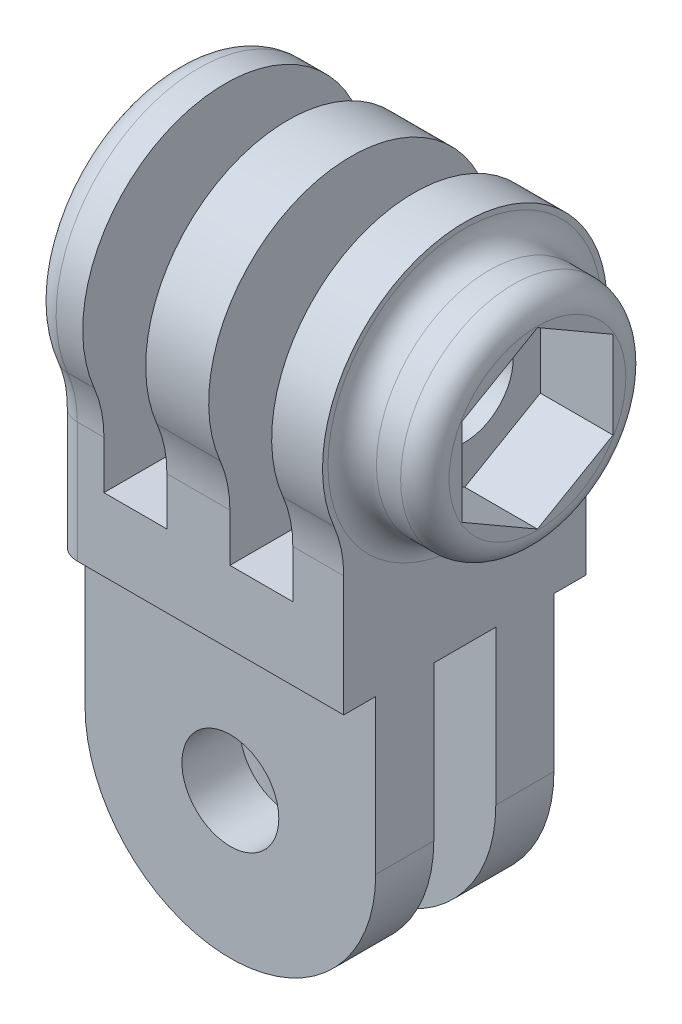
SolidWorks part; units mm, degrees
material "ABS"
ref_plane "Front Plane" through (0, 0, 0) normal (0, 0, 1) x (1, 0, 0)
ref_plane "Top Plane" through (0, 0, 0) normal (0, 1, 0) x (1, 0, 0)
ref_plane "Right Plane" through (0, 0, 0) normal (1, 0, 0) x (0, 0, -1)
sketch "Sketch1" plane through (0, 0, 0) normal (1, 0, 0) x (0, 0, -1)
  line L0 (-6.35, 0) -> (-4.6736, 0)
  line L1 (-6.35, 0) -> (-6.35, 6.3197)
  line L2 (6.35, 0) -> (6.35, 6.3197)
  line L3 (0, 0) -> (0, -15.7) construction
  line L4 (-1.6256, 0) -> (-1.6256, -15.7)
  line L5 (1.6256, 0) -> (1.6256, -15.7)
  line L6 (-4.6736, 0) -> (-4.6736, -15.7)
  line L7 (4.6736, 0) -> (4.6736, -15.7)
  line L8 (-4.6736, -15.7) -> (-1.6256, -15.7)
  line L9 (1.6256, -15.7) -> (4.6736, -15.7)
  line L10 (-1.6256, 0) -> (1.6256, 0)
  line L11 (4.6736, 0) -> (6.35, 0)
  circle A0 centre (0, 11.7475) radius 2.54
  arc A1 (6.8609, 8.8153) -> (-6.8609, 8.8153) centre (0, 11.7475) ccw
  arc A2 (6.8609, 8.8153) -> (6.35, 6.3197) centre (12.7, 6.3197) ccw
  arc A3 (-6.8609, 8.8153) -> (-6.35, 6.3197) centre (-12.7, 6.3197) cw
  dimension "D2" = 5.08
  dimension "D4" = 14.9225
  dimension "D5" = 6.35
  dimension "D1" = 12.7
  dimension "D3" = 11.7475
  dimension "D8" = 3.048
  dimension "D9" = 3.048
  dimension "D10" = 15.7
  dimension "D11" = 6.35
  dimension "D6" = 1.6256
  dimension "D7" = 1.6256
extrude "Boss-Extrude1" add sketch "Sketch1" against normal blind 15.24
sketch "Sketch2" plane through (0, 0, 4.6736) normal (0, 0, 1) x (1, 0, 0)
  line L0 (-7.62, 0) -> (-7.62, -15.7) construction
  line L1 (-15.24, 0) -> (0, 0) construction
  line L4 (-15.24, -8.08) -> (-15.24, 0)
  line L5 (-15.24, 0) -> (0, 0)
  line L6 (0, 0) -> (0, -8.08)
  line L7 (-15.24, -15.7) -> (0, -15.7) construction
  circle A0 centre (-7.62, -8.08) radius 2.54
  arc A1 (-15.24, -8.08) -> (0, -8.08) centre (-7.62, -8.08) ccw
  point P4 (-7.62, -15.7)
  line M1 (0, -15.7) -> (0, 0)
  line M3 (-15.24, 0) -> (-15.24, -15.7)
  line M4 (-15.24, -15.7) -> (0, -15.7)
  dimension "D1" = 5.08
extrude "Cut-Extrude1" cut sketch "Sketch2" against normal through all contours L0 A0 | A0 L0 | A1 M3 M4 | A1 M4 M1
sketch "Sketch3" plane through (0, 0, 0) normal (0, 0, 1) x (1, 0, 0)
  line L0 (0, 3.81) -> (-15.24, 3.81) construction
  line L1 (0, 6.3197) -> (0, 0) construction
  line L2 (-15.24, 6.3197) -> (-15.24, 0) construction
  line L3 (-15.24, 0) -> (0, 0) construction
  line L4 (-7.62, 3.81) -> (-7.62, 19.2088) construction
  line L5 (0, 19.2088) -> (-15.24, 19.2088) construction
  line L6 (-5.969, 3.81) -> (-5.969, 19.2088)
  line L7 (-9.271, 3.81) -> (-9.271, 19.2088)
  line L8 (-9.271, 19.2088) -> (-12.573, 19.2088)
  line L9 (-9.271, 3.81) -> (-12.573, 3.81)
  line L10 (-12.573, 3.81) -> (-12.573, 19.2088)
  line L11 (-5.969, 3.81) -> (-2.667, 3.81)
  line L12 (-2.667, 3.81) -> (-2.667, 19.2088)
  line L13 (-5.969, 19.2088) -> (-2.667, 19.2088)
  dimension "D1" = 3.81
  dimension "D4" = 3.302
  dimension "D5" = 3.302
  dimension "D2" = 1.651
  dimension "D3" = 1.651
extrude "Cut-Extrude2" cut sketch "Sketch3" against normal through all and the other way through all
sketch "Sketch5" plane through (0, 0, 0) normal (1, 0, 0) x (0, 0, -1)
  circle A0 centre (0, 11.7475) radius 5.9055
  circle A1 centre (0, 11.7475) radius 2.54
  circle A2 centre (0, 11.7475) radius 2.54 construction
  dimension "D1" = 11.811
extrude "Boss-Extrude2" add sketch "Sketch5" along normal blind 3.81
sketch "Sketch6" plane through (3.81, 0, 0) normal (1, 0, 0) x (0, 0, -1)
  line L1 (0, 16.3229) -> (-3.9624, 14.0352)
  line L2 (-3.9624, 14.0352) -> (-3.9624, 9.4598)
  line L3 (-3.9624, 9.4598) -> (0, 7.1721)
  line L4 (0, 7.1721) -> (3.9624, 9.4598)
  line L5 (3.9624, 9.4598) -> (3.9624, 14.0352)
  line L6 (3.9624, 14.0352) -> (0, 16.3229)
  circle A0 centre (0, 11.7475) radius 3.9624 construction
  dimension "D1" = 7.9248
extrude "Cut-Extrude3" cut sketch "Sketch6" against normal up to surface (3.81 mm away) up to face at (0, 0.5997, 0)
fillet "Fillet1" radius 1.27 7 edges at (-15.24, 3.1599, -6.35) (-15.24, 7.5934, -6.479) (-15.24, 3.1599, 6.35) (-15.24, 7.5934, 6.479) (-15.24, 19.2088, 0) (0, 11.7475, 5.9055) (3.81, 11.7475, -5.9055)
